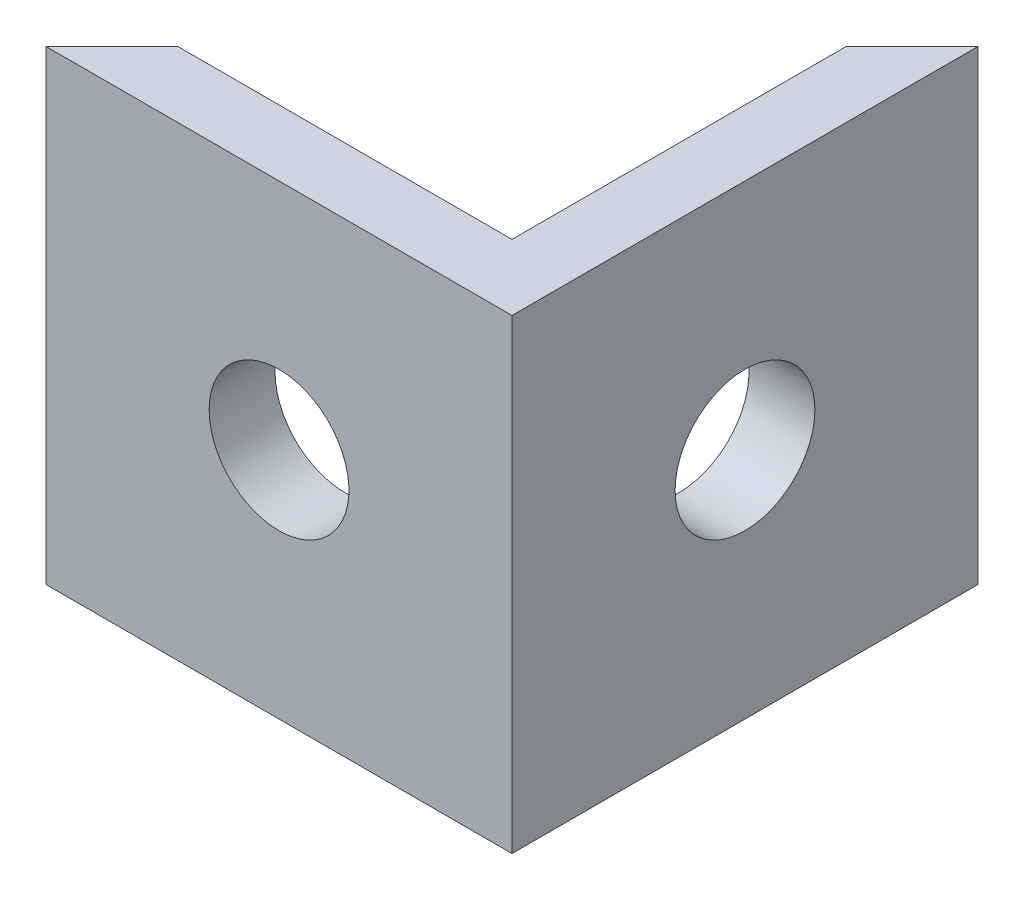
SolidWorks part; units mm, degrees
ref_plane "Front Plane" through (0, 0, 0) normal (0, 0, 1) x (1, 0, 0)
ref_plane "Top Plane" through (0, 0, 0) normal (0, 1, 0) x (1, 0, 0)
ref_plane "Right Plane" through (0, 0, 0) normal (1, 0, 0) x (0, 0, -1)
sketch "Çizim1" plane through (0, 0, 0) normal (0, 1, 0) x (1, 0, 0)
  line L1 (-28.6405, -22.2856) -> (-18.6405, -22.2856)
  line L2 (-28.6405, -22.2856) -> (-28.6405, -32.2856)
  line L3 (-28.6405, -32.2856) -> (-18.6405, -32.2856)
  line L4 (-18.6405, -22.2856) -> (-18.6405, -32.2856)
extrude "Yükseklik-Ekstrüzyon1" add sketch "Çizim1" along normal blind 10 contours L2 L1 L4 L3
sketch "Çizim2" plane through (0, 10, 0) normal (0, 1, 0) x (1, 0, 0)
  line L0 (-28.6405, -22.2856) -> (-18.6405, -22.2856)
  line L1 (-18.6405, -22.2856) -> (-28.6405, -32.2856)
  line L2 (-28.6405, -32.2856) -> (-28.6405, -22.2856)
extrude "Kes-Ekstrüzyon1" cut sketch "Çizim2" against normal blind 10
sketch "Çizim3" plane through (0, 10, 0) normal (0, 1, 0) x (1, 0, 0)
  line L0 (-18.6405, -32.2856) -> (-20.0547, -30.8714)
  line L2 (-20.0547, -30.8714) -> (-29.2817, -30.8714)
  line L3 (-20.0547, -30.8714) -> (-20.0547, -21.9794)
  line L4 (-20.0547, -21.9794) -> (-29.2817, -21.9794)
  line L5 (-29.2817, -30.8714) -> (-29.2817, -21.9794)
extrude "Kes-Ekstrüzyon2" cut sketch "Çizim3" against normal blind 10 contours L3 L2 L5 L4
sketch "Çizim5" plane through (-20.0547, 0, 0) normal (-1, 0, 0) x (0, 0, 1)
  line L0 (23.6999, 10) -> (30.8714, 0)
  circle A0 centre (27.2856, 5) radius 1.5
extrude "Kes-Ekstrüzyon3" cut sketch "Çizim5" against normal blind 10 contours L0 A0 | L0 A0
sketch "Çizim6" plane through (0, 0, 30.8714) normal (0, 0, -1) x (-1, 0, 0)
  line L0 (20.0547, 10) -> (27.2263, 0) construction
  circle A0 centre (23.6405, 5) radius 1.5
extrude "Kes-Ekstrüzyon4" cut sketch "Çizim6" against normal blind 10
